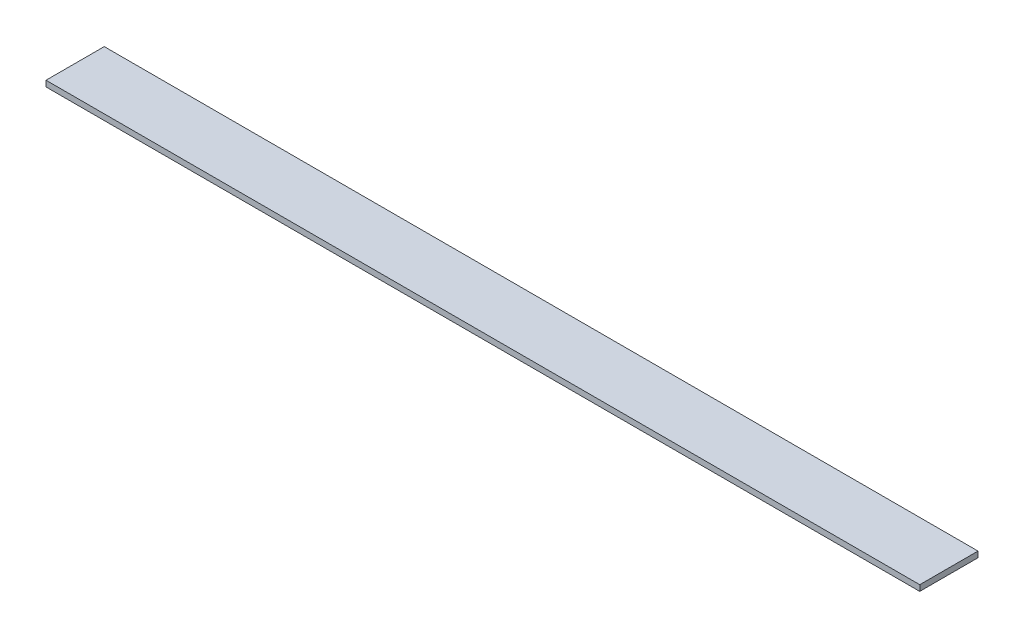
SolidWorks part; units mm, degrees
ref_plane "Спереди" through (0, 0, 0) normal (0, 0, 1) x (1, 0, 0)
ref_plane "Сверху" through (0, 0, 0) normal (0, 1, 0) x (1, 0, 0)
ref_plane "Справа" through (0, 0, 0) normal (1, 0, 0) x (0, 0, -1)
sketch "Эскиз1" plane through (0, 0, 0) normal (0, 1, 0) x (1, 0, 0)
  line L1 (0, 0) -> (450, 0)
  line L2 (0, 0) -> (0, 30)
  line L3 (0, 30) -> (450, 30)
  line L4 (450, 0) -> (450, 30)
extrude "Бобышка-Вытянуть1" add sketch "Эскиз1" along normal blind 3
